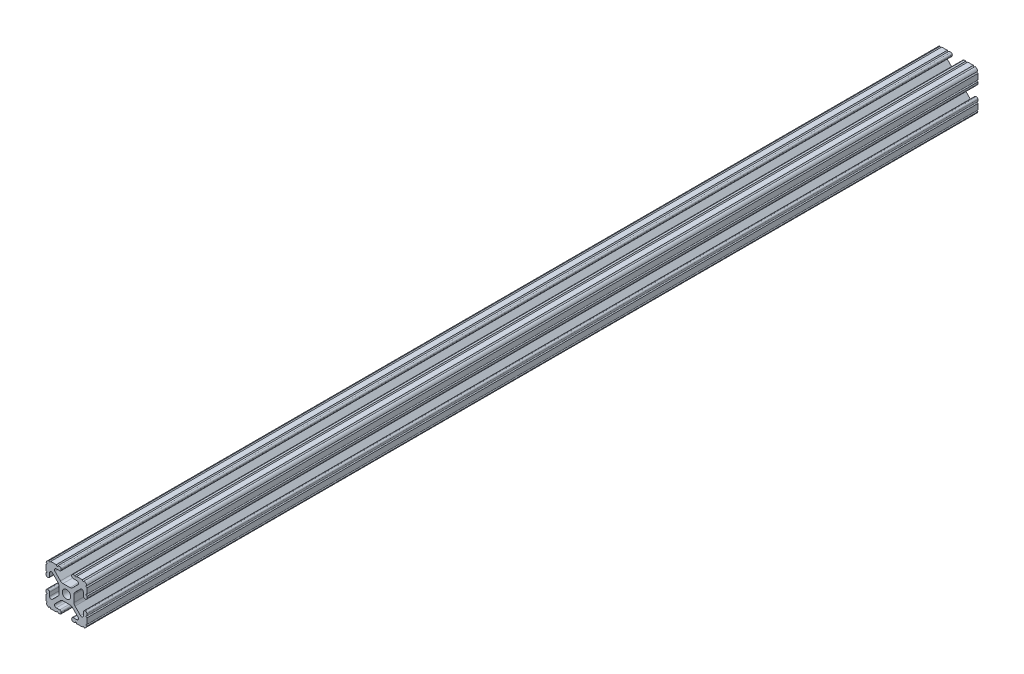
SolidWorks part; units mm, degrees
ref_plane "Front Plane" through (0, 0, 0) normal (0, 0, 1) x (1, 0, 0)
ref_plane "Top Plane" through (0, 0, 0) normal (0, 1, 0) x (1, 0, 0)
ref_plane "Right Plane" through (0, 0, 0) normal (1, 0, 0) x (0, 0, -1)
sketch "Sketch2" plane through (0, 0, 0) normal (0, 0, 1) x (1, 0, 0)
  line L0 (0, 12.7) -> (0, -12.7) construction
  line L1 (-12.7, 0) -> (12.7, 0) construction
  line L2 (3.2512, -12.7) -> (12.7, -12.7)
  line L3 (12.7, -12.7) -> (12.7, -3.2512)
  line L4 (3.2512, -12.7) -> (3.2512, -10.4902)
  line L5 (3.2512, -10.4902) -> (8.9276, -10.4902)
  line L6 (8.9276, -10.4902) -> (3.0856, -4.6482)
  line L7 (0, 0) -> (12.7, -12.7) construction
  line L8 (12.7, -3.2512) -> (10.4902, -3.2512)
  line L9 (10.4902, -3.2512) -> (10.4902, -8.9276)
  line L10 (10.4902, -8.9276) -> (4.6482, -3.0856)
  circle A0 centre (0, 0) radius 2.6035
  arc A1 (6.3485, -10.4902) -> (7.1039, -8.6665) centre (6.3485, -9.4219) ccw construction
  point P8 (0, -4.6482)
  dimension "Center Hole Diameter" = 5.207
  dimension "Rail Height" = 25.4
  dimension "Rail Width" = 25.4
  dimension "T-Slot Width" = 6.5024
  dimension "Slot Inner Width" = 14.8336
  dimension "Thickness" = 2.2098
  dimension "Slot Depth" = 5.842
  dimension "D1" = 2.2098
sketch "Sketch3" plane through (0, 0, 0) normal (1, 0, 0) x (0, 0, -1)
  line L0 (-304.8, -12.7) -> (304.8, -12.7) construction
  line L1 (-279.4, 0) -> (279.4, 0) construction
  dimension "Length" = 609.6
  dimension "D1" = 25.4
sketch "Sketch4" plane through (0, 0, 0) normal (0, 0, 1) x (1, 0, 0)
  line L0 (4.1904, -12.7) -> (10.1173, -12.7)
  line L1 (3.2512, -12.7) -> (12.7, -12.7) construction
  line L2 (3.2512, -12.7) -> (3.2512, -10.4902) construction
  line L3 (3.2512, -10.4902) -> (8.9276, -10.4902) construction
  line L4 (3.2512, -11.4294) -> (3.2512, -11.7608)
  line L5 (4.1904, -10.4902) -> (6.3485, -10.4902)
  line L6 (0, -4.6482) -> (2.164, -4.6482)
  line L7 (8.9276, -10.4902) -> (3.0856, -4.6482) construction
  line L8 (3.7373, -5.2999) -> (7.1039, -8.6665)
  line L9 (12.7, -12.7) -> (12.7, -3.2512) construction
  line L10 (10.4902, -8.9276) -> (4.6482, -3.0856) construction
  line L11 (10.4902, -3.2512) -> (10.4902, -8.9276) construction
  line L12 (10.4902, -6.3485) -> (10.4902, -4.1904)
  line L13 (12.7, -3.2512) -> (10.4902, -3.2512) construction
  line L14 (11.4294, -3.2512) -> (11.7608, -3.2512)
  line L15 (12.7, -4.1904) -> (12.7, -10.1173)
  line L16 (8.6665, -7.1039) -> (5.2999, -3.7373)
  line L17 (4.6482, 0) -> (4.6482, -2.164)
  line L18 (-12.7, 0) -> (12.7, 0) construction
  line L19 (0, -4.6482) -> (0, -2.6035)
  line L20 (0, 12.7) -> (0, -12.7) construction
  line L21 (4.6482, 0) -> (2.6035, 0)
  arc A0 (3.2512, -11.7608) -> (4.1904, -12.7) centre (4.1904, -11.7608) ccw
  arc A2 (3.2512, -11.4294) -> (4.1904, -10.4902) centre (4.1904, -11.4294) cw
  arc A3 (6.3485, -10.4902) -> (7.1039, -8.6665) centre (6.3485, -9.4219) ccw
  arc A4 (2.164, -4.6482) -> (3.7373, -5.2999) centre (2.164, -6.8732) cw
  arc A5 (10.1173, -12.7) -> (12.7, -10.1173) centre (10.1173, -10.1173) ccw
  arc A6 (8.6665, -7.1039) -> (10.4902, -6.3485) centre (9.4219, -6.3485) ccw
  arc A7 (10.4902, -4.1904) -> (11.4294, -3.2512) centre (11.4294, -4.1904) cw
  arc A8 (11.7608, -3.2512) -> (12.7, -4.1904) centre (11.7608, -4.1904) cw
  arc A9 (5.2999, -3.7373) -> (4.6482, -2.164) centre (6.8732, -2.164) cw
  circle A10 centre (0, 0) radius 2.6035 construction
  arc A11 (0, -2.6035) -> (2.6035, 0) centre (0, 0) ccw
  dimension "D1" = 2.5827
  dimension "D2" = 2.225
  dimension "D3" = 0.9392
extrude "Boss-Extrude1" add sketch "Sketch4" along normal mid plane 609.6
sketch "Sketch5" plane through (0, 0, 0) normal (0, 0, 1) x (1, 0, 0)
  line L0 (3.2512, -12.7) -> (12.7, -12.7) construction
  line L1 (4.1904, -10.4902) -> (6.3485, -10.4902) construction
  line L3 (0, 0) -> (12.7, -12.7) construction
  line L4 (6.3485, -10.4902) -> (6.3485, -12.7) construction
  line L5 (8.9276, -10.4902) -> (3.0856, -4.6482) construction
  circle A0 centre (10.3562, -12.7) radius 0.5524
  circle A1 centre (5.796, -12.7) radius 0.5524
  circle A2 centre (12.7, -10.3562) radius 0.5524
  circle A3 centre (12.7, -5.796) radius 0.5524
  point P10 (5.2694, -10.4902)
  point P12 (9.4219, -6.3485)
  dimension "D1" = 1.1049
extrude "Cut-Extrude1" cut sketch "Sketch5" against normal through all both and the other way through all
mirror "Mirror1" about plane through (0, 0, 0) normal (1, 0, 0) of bodies 137 134
mirror "Mirror2" about plane through (0, 0, 0) normal (0, 1, 0) of bodies 135
sketch "Sketch6" plane through (0, 0, 0) normal (0, 1, 0) x (1, 0, 0)
  line L1 (-15.935, -304.8) -> (15.815, -304.8)
  line L2 (-15.935, -304.8) -> (-15.935, -247.65)
  line L3 (-15.935, -247.65) -> (15.815, -247.65)
  line L4 (15.815, -304.8) -> (15.815, -247.65)
  line L5 (-12.7, -284.492) -> (12.58, -284.492) construction
  line L6 (-12.7, -304.8) -> (-12.7, 304.8) construction
  line L7 (12.58, 304.8) -> (12.58, -304.8) construction
  point P11 (-0.06, -284.492)
  point P12 (-0.06, -304.8)
  dimension "D1" = 57.15
  dimension "D2" = 31.75
extrude "Cut-Extrude2" cut sketch "Sketch6" against normal mid plane 25.4
equation "\"D1@Boss-Extrude1\"=\"Length@Sketch3\""
equation "\"D1@Sketch2\"=\"Thickness@Sketch2\""
equation "\"D2@Sketch4\"=\"Slot Inner Width@Sketch2\"*0.15"
equation "\"D1@Sketch4\"=\"D3@Sketch4\"*2.75"
equation "\"D3@Sketch4\"=\"Thickness@Sketch2\"*0.425"
equation "\"D1@Sketch5\"=\"Thickness@Sketch2\"*0.5"
